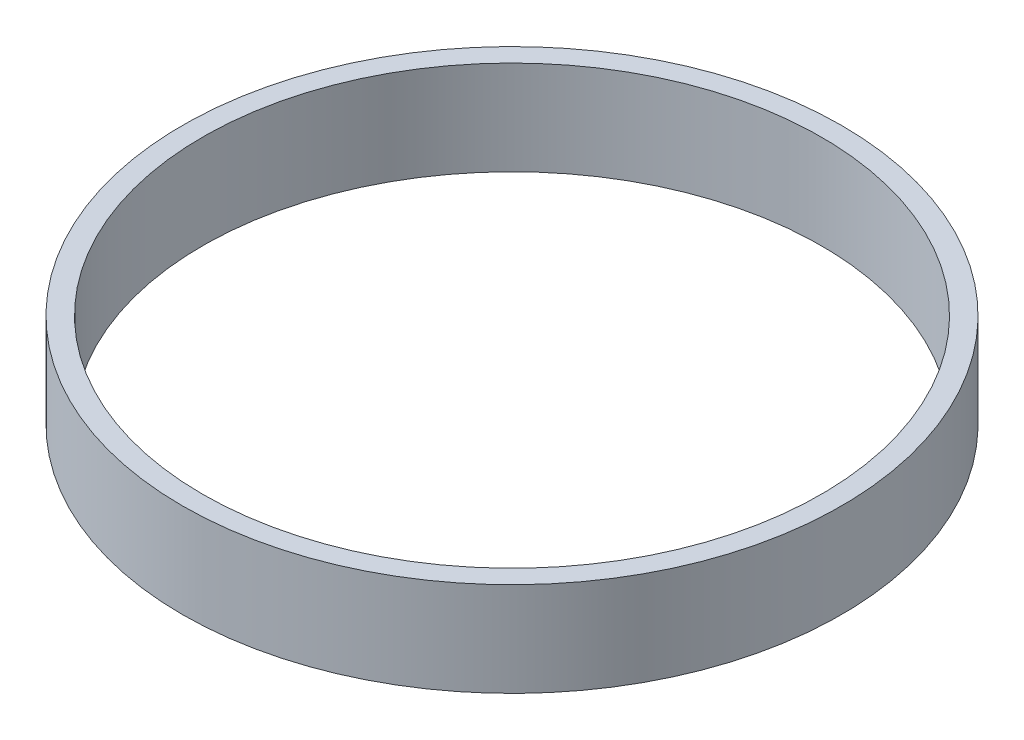
SolidWorks part; units mm, degrees
ref_plane "Front Plane" through (0, 0, 0) normal (0, 0, 1) x (1, 0, 0)
ref_plane "Top Plane" through (0, 0, 0) normal (0, 1, 0) x (1, 0, 0)
ref_plane "Right Plane" through (0, 0, 0) normal (1, 0, 0) x (0, 0, -1)
sketch "Sketch1" plane through (0, 0, 0) normal (0, 1, 0) x (1, 0, 0)
  circle A0 centre (0, 0) radius 23
  circle A1 centre (0, 0) radius 24.5
extrude "Boss-Extrude1" add sketch "Sketch1" along normal blind 7
